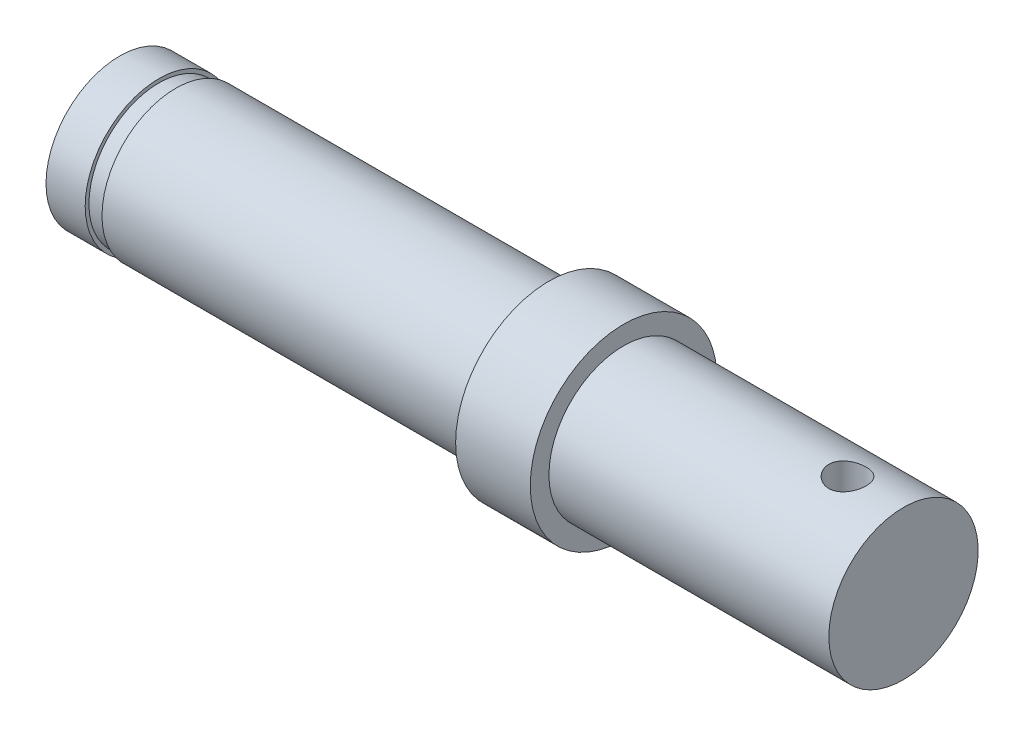
SolidWorks part; units mm, degrees
material "6061 合金"
ref_plane "前视基准面" through (0, 0, 0) normal (0, 0, 1) x (1, 0, 0)
ref_plane "上视基准面" through (0, 0, 0) normal (0, 1, 0) x (1, 0, 0)
ref_plane "右视基准面" through (0, 0, 0) normal (1, 0, 0) x (0, 0, -1)
sketch "草图1" plane through (0, 0, 0) normal (0, 0, 1) x (1, 0, 0)
  line L0 (-15.4994, 0) -> (26.5006, 0)
  line L1 (26.5006, 0) -> (26.5006, 4)
  line L2 (26.5006, 4) -> (11.5006, 4)
  line L3 (11.5006, 4) -> (11.5006, 5)
  line L4 (11.5006, 5) -> (7.5006, 5)
  line L5 (7.5006, 5) -> (7.5006, 3.95)
  line L6 (7.5006, 3.95) -> (-12.4994, 3.95)
  line L7 (-15.4994, 3.95) -> (-15.4994, 0)
  line L8 (-13.3994, 3.95) -> (-13.3994, 3.75)
  line L9 (-13.3994, 3.75) -> (-12.4994, 3.75)
  line L10 (-12.4994, 3.75) -> (-12.4994, 3.95)
  line L11 (-13.3994, 3.95) -> (-15.4994, 3.95)
  dimension "D1" = 0.9
  dimension "D2" = 0.2
  dimension "D3" = 3.95
  dimension "D4" = 5
  dimension "D5" = 15
  dimension "D6" = 4
  dimension "D7" = 23
  dimension "D8" = 20
  dimension "D9" = 4
revolve "旋转1" add sketch "草图1" angle 360 about L0
sketch "草图2" plane through (0, 0, 0) normal (0, 1, 0) x (1, 0, 0)
  line L0 (-21.8469, 0) -> (35.0006, 0) construction
  line L1 (11.5006, -5) -> (11.5006, 5) construction
  circle A0 centre (23.5006, 0) radius 1
  dimension "D1" = 2
  dimension "D2" = 12
extrude "切除-拉伸1" cut sketch "草图2" against normal mid plane 10
